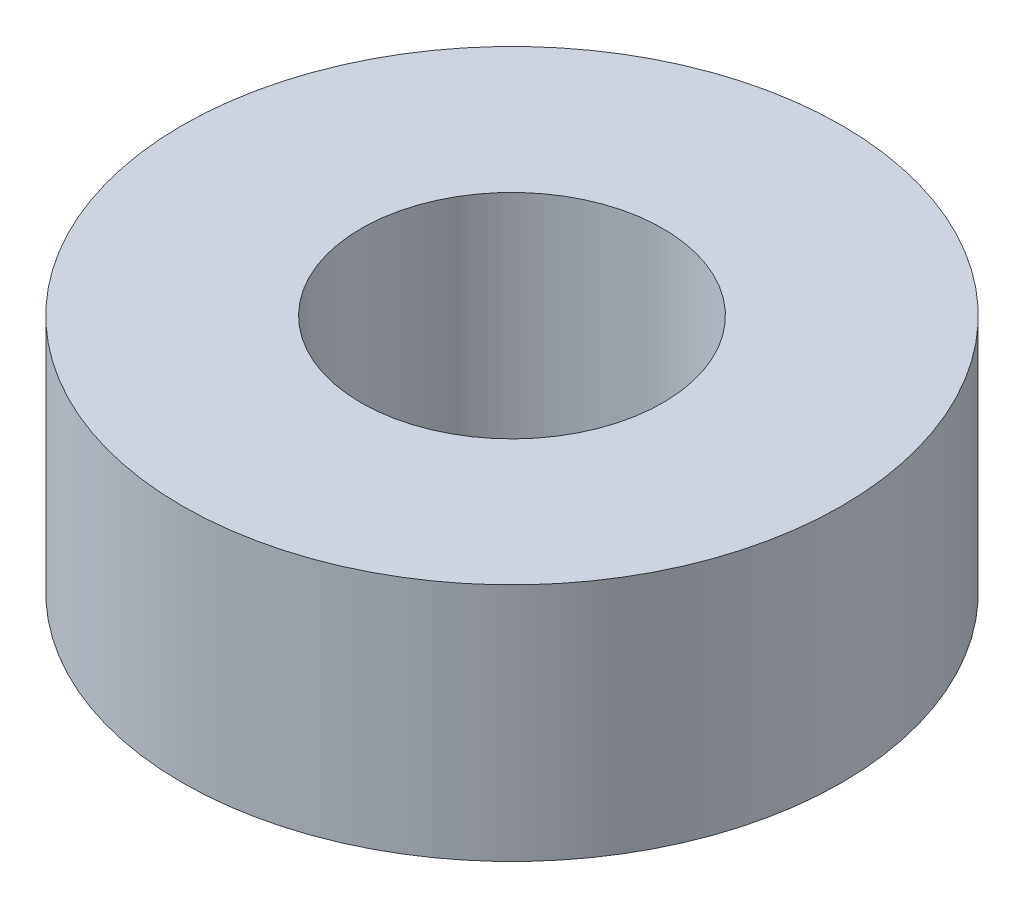
SolidWorks part; units mm, degrees
material "6061-T6 (SS)"
ref_plane "Front Plane" through (0, 0, 0) normal (0, 0, 1) x (1, 0, 0)
ref_plane "Top Plane" through (0, 0, 0) normal (0, 1, 0) x (1, 0, 0)
ref_plane "Right Plane" through (0, 0, 0) normal (1, 0, 0) x (0, 0, -1)
sketch "Sketch1" plane through (0, 0, 0) normal (0, 1, 0) x (1, 0, 0)
  circle A0 centre (0, 0) radius 4.0005
  circle A1 centre (0, 0) radius 8.7376
  dimension "D1" = 8.001
  dimension "D2" = 17.4752
extrude "Boss-Extrude1" add sketch "Sketch1" along normal blind 6.35
